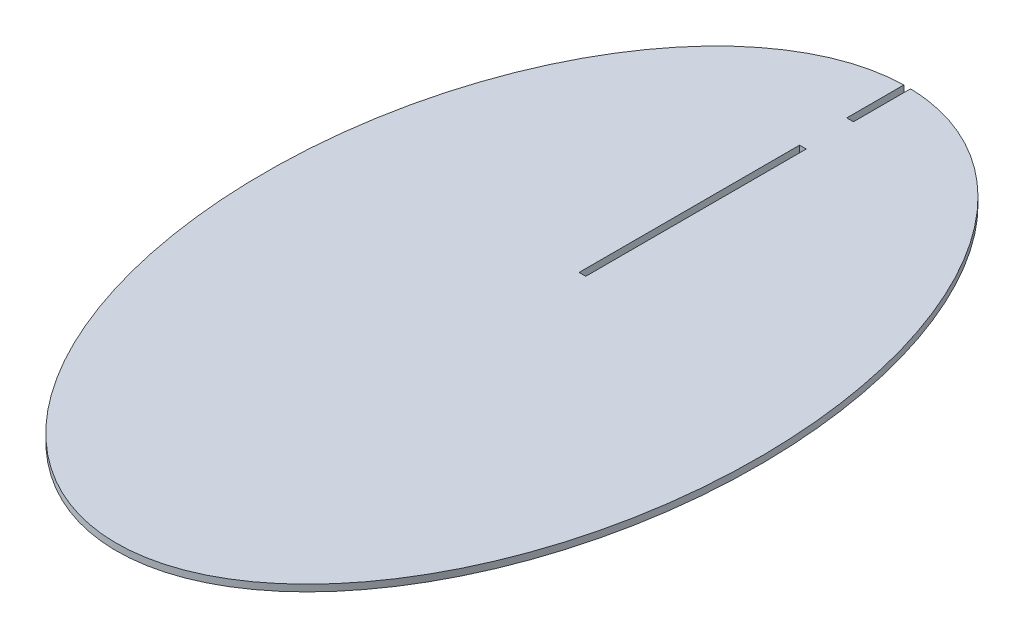
SolidWorks part; units mm, degrees
ref_plane "Front Plane" through (0, 0, 0) normal (0, 0, 1) x (1, 0, 0)
ref_plane "Top Plane" through (0, 0, 0) normal (0, 1, 0) x (1, 0, 0)
ref_plane "Right Plane" through (0, 0, 0) normal (1, 0, 0) x (0, 0, -1)
sketch "Sketch1" plane through (0, 0, 0) normal (0, 1, 0) x (1, 0, 0)
  line L0 (0, 93.625) -> (0, 77.0678) construction
  line L1 (-0.762, 90.0845) -> (-0.762, 77.0678)
  line L2 (0, 66.3202) -> (0, 16.0748) construction
  line L3 (-0.762, 66.3202) -> (-0.762, 16.0748)
  line L4 (0.762, 90.0845) -> (0.762, 77.0678)
  line L5 (0.762, 66.3202) -> (0.762, 16.0748)
  line L7 (-0.762, 77.0678) -> (0.762, 77.0678)
  line L8 (-0.762, 66.3202) -> (0.762, 66.3202)
  line L9 (-0.762, 16.0748) -> (0.762, 16.0748)
  line L11 (-0.762, 93.625) -> (-0.762, 77.0678) construction
  line L12 (0.762, 93.625) -> (0.762, 77.0678) construction
  ellipse E0 centre (0, 0) end of major axis (0, 90.0927) minor radius 56.2692 (-0.762, 90.0845) -> (0.762, 90.0845) ccw
  dimension "D1" = 0.762
  dimension "D2" = 0.762
extrude "Boss-Extrude1" add sketch "Sketch1" along normal blind 1.524
